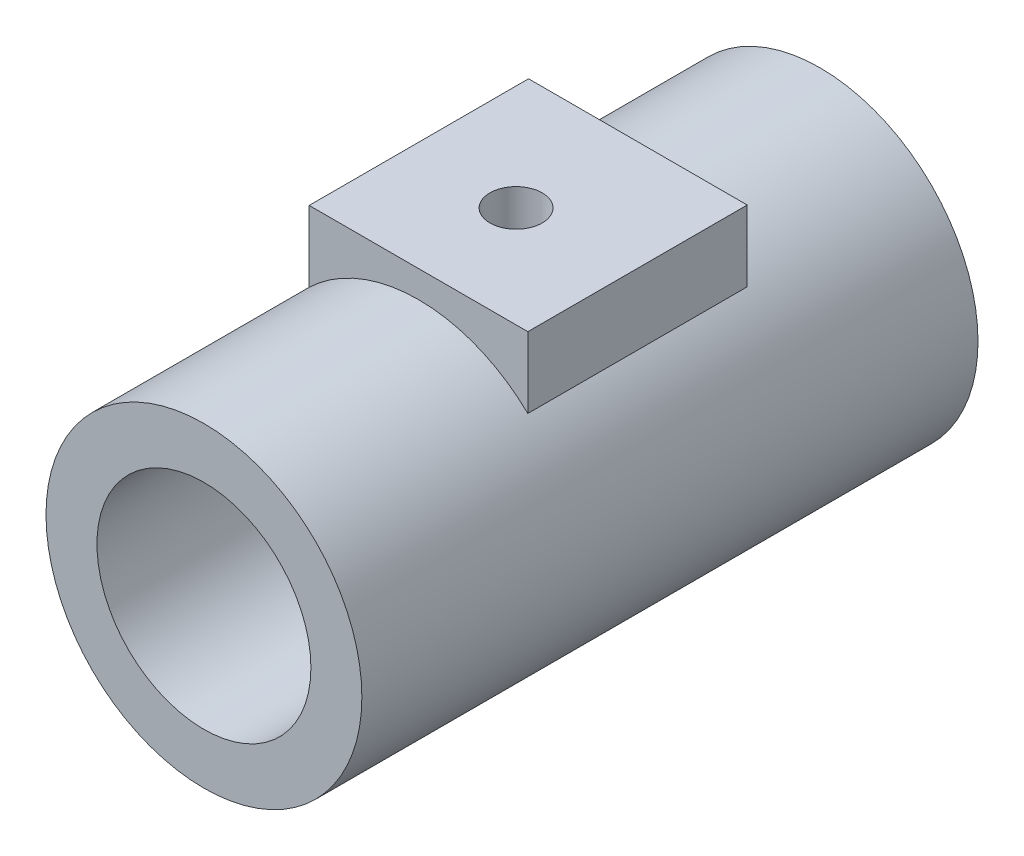
SolidWorks part; units mm, degrees
ref_plane "Front Plane" through (0, 0, 0) normal (0, 0, 1) x (1, 0, 0)
ref_plane "Top Plane" through (0, 0, 0) normal (0, 1, 0) x (1, 0, 0)
ref_plane "Right Plane" through (0, 0, 0) normal (1, 0, 0) x (0, 0, -1)
sketch "Sketch16" plane through (0, 0, 0) normal (0, 0, 1) x (1, 0, 0)
  circle A0 centre (0, 0) radius 38.4485
extrude "Boss-Extrude3" add sketch "Sketch16" along normal blind 150
sketch "Sketch17" plane through (0, 0, 150) normal (0, 0, 1) x (1, 0, 0)
  circle A0 centre (0, 0) radius 26.0463
extrude "Cut-Extrude2" cut sketch "Sketch17" against normal through all both and the other way through all
sketch "Sketch18" plane through (0, 0, 0) normal (0, 1, 0) x (1, 0, 0)
  circle A0 centre (0, -71.0551) radius 18.6856
extrude "Cut-Extrude3" cut sketch "Sketch18" against normal blind 1 and the other way through all
sketch "Sketch19" plane through (0, 0, 0) normal (0, 1, 0) x (1, 0, 0)
  line L1 (-26.6144, -44.3513) -> (26.6144, -44.3513)
  line L2 (-26.6144, -44.3513) -> (-26.6144, -97.7589)
  line L3 (-26.6144, -97.7589) -> (26.6144, -97.7589)
  line L4 (26.6144, -44.3513) -> (26.6144, -97.7589)
  line L5 (-26.6144, -44.3513) -> (26.6144, -97.7589) construction
  line L6 (-26.6144, -97.7589) -> (26.6144, -44.3513) construction
  point P0 (0, -71.0551)
extrude "Boss-Extrude4" add sketch "Sketch19" along normal blind 45 and the other way blind 1
sketch "Sketch20" plane through (0, 0, 0) normal (0, 1, 0) x (1, 0, 0)
  circle A0 centre (0, -71.0551) radius 22.4883
  point P2 (0, -70.8124)
  point P3 (0, -71.0551)
extrude "Cut-Extrude4" cut sketch "Sketch20" against normal blind 1 and the other way through all
sketch "Sketch21" plane through (0, 0, 0) normal (0, 1, 0) x (1, 0, 0)
  line L1 (-26.6144, -44.7154) -> (26.6144, -44.7154)
  line L2 (-26.6144, -44.7154) -> (-26.6144, -97.7589)
  line L3 (-26.6144, -97.7589) -> (26.6144, -97.7589)
  line L4 (26.6144, -44.7154) -> (26.6144, -97.7589)
  line L5 (-26.6144, -44.7154) -> (26.6144, -97.7589) construction
  line L6 (-26.6144, -97.7589) -> (26.6144, -44.7154) construction
  point P0 (0, -71.2372)
extrude "Boss-Extrude5" add sketch "Sketch21" along normal blind 45
sketch "Sketch22" plane through (0, 0, 0) normal (0, 1, 0) x (1, 0, 0)
  circle A0 centre (-0.9057, -73.1051) radius 6.3641
  point P2 (0, -72.0262)
  point P3 (-1.1203, -73.5442)
  point P4 (-0.9057, -73.1051)
extrude "Cut-Extrude5" cut sketch "Sketch22" along normal blind 55 and the other way blind 1
